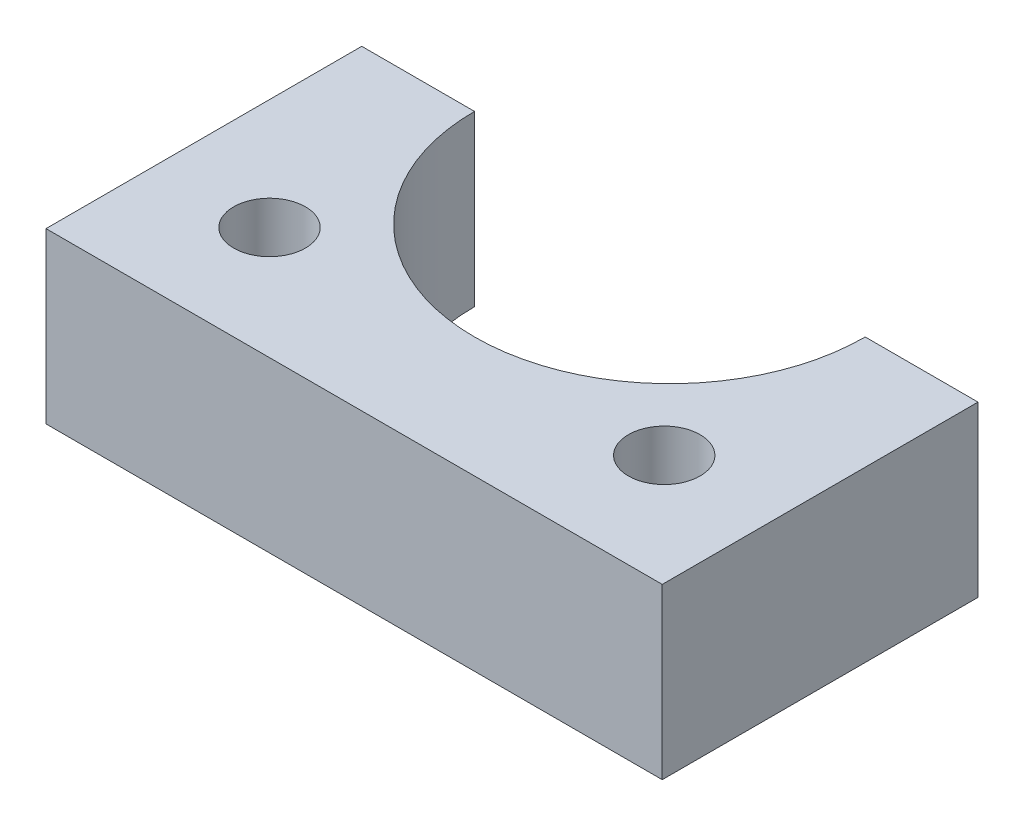
SolidWorks part; units mm, degrees
material "Alum Plate"
ref_plane "Front Plane" through (0, 0, 0) normal (0, 0, 1) x (1, 0, 0)
ref_plane "Top Plane" through (0, 0, 0) normal (0, 1, 0) x (1, 0, 0)
ref_plane "Right Plane" through (0, 0, 0) normal (1, 0, 0) x (0, 0, -1)
other "Bounding Box"
ref_plane "Default Plane" through (-8.9266, -12.7485, 0) normal (-0.1736, 0.9848, 0) x (0.9848, 0.1736, 0)
sketch "Sketch1" plane through (0, 0, 0) normal (0, 1, 0) x (1, 0, 0)
  line L0 (-11, 0) -> (-11, -17.78) construction
  line L1 (-11, -17.78) -> (11, -17.78)
  line L2 (11, -17.78) -> (11, 0) construction
  line L3 (-11, -17.78) -> (-17.35, -17.78)
  line L4 (-17.35, -17.78) -> (-17.35, 0)
  line L5 (-17.35, 0) -> (-11, 0)
  line L6 (11, 0) -> (17.35, 0)
  line L7 (17.35, 0) -> (17.35, -17.78)
  line L8 (17.35, -17.78) -> (11, -17.78)
  arc A0 (-11, 0) -> (11, 0) centre (0, 0) ccw
  dimension "D2" = 11
  dimension "D1" = 17.78
  dimension "D3" = 6.35
extrude "Boss-Extrude1" add sketch "Sketch1" along normal blind 9.525
sketch "Sketch2" plane through (0, 9.525, 0) normal (0, 1, 0) x (1, 0, 0)
  line L0 (0, -17.78) -> (0, -13.97) construction
  line L1 (2.7496, -9.2075) -> (-2.7496, -9.2075)
  line L2 (-2.7496, -9.2075) -> (-5.4993, -13.97)
  line L3 (-5.4993, -13.97) -> (-2.7496, -18.7325)
  line L4 (-2.7496, -18.7325) -> (2.7496, -18.7325)
  line L5 (2.7496, -18.7325) -> (5.4993, -13.97)
  line L6 (5.4993, -13.97) -> (2.7496, -9.2075)
  line L7 (-17.35, -17.78) -> (17.35, -17.78) construction
  circle A0 centre (0, -13.97) radius 4.7625 construction
  point P9 (0, -15.1631)
  dimension "D1" = 9.525
  dimension "D2" = 3.81
sketch "Sketch3" plane through (0, 9.525, 0) normal (0, 1, 0) x (1, 0, 0)
  line L0 (-11.1125, -11.43) -> (11.1125, -11.43) construction
  line L1 (0, -11.43) -> (0, -17.78) construction
  line L2 (-17.35, -17.78) -> (17.35, -17.78) construction
  circle A0 centre (11.1125, -11.43) radius 2.0193
  circle A1 centre (-11.1125, -11.43) radius 2.0193
  dimension "D1" = 4.0386
  dimension "D2" = 22.225
  dimension "D3" = 6.35
extrude "Cut-Extrude2" cut sketch "Sketch3" against normal through all
